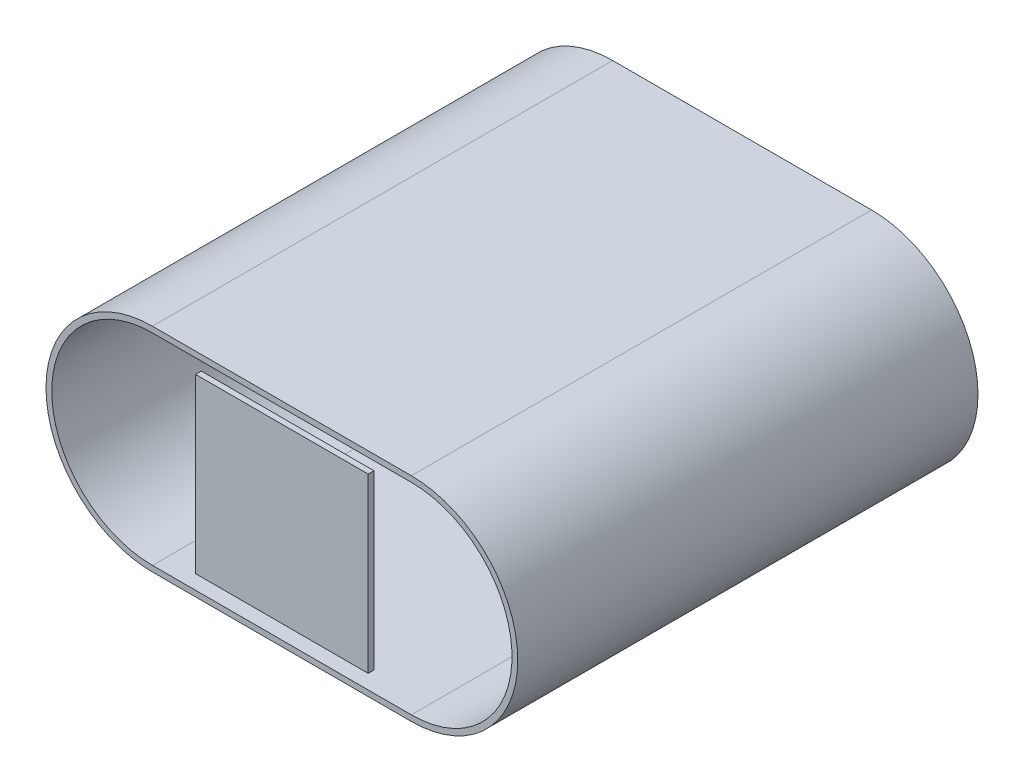
SolidWorks part; units mm, degrees
other "COLL.BOX-Boss-Extrude5"
other "COLL.BOX-Boss-Extrude4"
other "COLL.BOX-Boss-Extrude2"
ref_plane "Front Plane" through (0, 0, 0) normal (0, 0, 1) x (1, 0, 0)
ref_plane "Top Plane" through (0, 0, 0) normal (0, 1, 0) x (1, 0, 0)
ref_plane "Right Plane" through (0, 0, 0) normal (1, 0, 0) x (0, 0, -1)
sketch "Sketch1" plane through (0, 0, 0) normal (0, 0, 1) x (1, 0, 0)
  line L1 (-22.5, -18.5) -> (22.5, -18.5)
  line L2 (-22.5, -18.5) -> (-22.5, 18.5)
  line L3 (-22.5, 18.5) -> (22.5, 18.5)
  line L4 (22.5, -18.5) -> (22.5, 18.5)
  line L5 (-22.5, -18.5) -> (22.5, 18.5) construction
  line L6 (-22.5, 18.5) -> (22.5, -18.5) construction
  arc A0 (-22.5, 18.5) -> (-22.5, -18.5) centre (-22.5, 0) ccw
  arc A1 (22.5, 18.5) -> (22.5, -18.5) centre (22.5, 0) cw
  point P0 (0, 0)
  dimension "D1" = 37
  dimension "D2" = 45
extrude "Boss-Extrude1" add sketch "Sketch1" along normal blind 80 contours L1 L4 L3 L2 | A1 L4 | L2 A0
shell "Shell1" thickness 1
sketch "Sketch2" plane through (0, 0, 0) normal (0, 0, -1) x (-1, 0, 0)
  line L1 (-22.5, -17.5) -> (22.5, -17.5)
  line L2 (-22.5, -17.5) -> (-22.5, 17.5)
  line L3 (-22.5, 17.5) -> (22.5, 17.5)
  line L4 (22.5, -17.5) -> (22.5, 17.5)
  line L5 (-22.5, -17.5) -> (22.5, 17.5) construction
  line L6 (-22.5, 17.5) -> (22.5, -17.5) construction
  point P0 (0, 0)
  dimension "D1" = 35
  dimension "D2" = 45
extrude "Boss-Extrude2" add sketch "Sketch2" against normal blind 1 separate body
sketch "Sketch3" plane through (0, 0, 0) normal (0, 0, -1) x (-1, 0, 0)
  circle A0 centre (0, 0) radius 1.25
  dimension "D1" = 2.5
extrude "Boss-Extrude3" add sketch "Sketch3" along normal blind 15
ref_plane "Plane1" through (0, 0, -15) normal (0, 0, -1) x (-1, 0, 0)
ref_point "Point1"
sketch "Sketch5" plane through (0, 0, -15) normal (0, 0, -1) x (-1, 0, 0)
  line L0 (0, 2.4986) -> (0, -2.4986)
  arc A0 (0, 2.4986) -> (0, -2.4986) centre (0, 0) ccw
  dimension "D1" = 2.4986
revolve "Revolve1" add sketch "Sketch5" angle 360 about L0
sketch "Sketch6" plane through (0, 0, 0) normal (0, 0, -1) x (-1, 0, 0)
  line L1 (-22.5, -17.5) -> (22.5, -17.5)
  line L2 (-22.5, -17.5) -> (-22.5, 17.5)
  line L3 (-22.5, 17.5) -> (22.5, 17.5)
  line L4 (22.5, -17.5) -> (22.5, 17.5)
  line L5 (-22.5, -17.5) -> (22.5, 17.5) construction
  line L6 (-22.5, 17.5) -> (22.5, -17.5) construction
  point P0 (0, 0)
  dimension "D1" = 35
  dimension "D2" = 45
extrude "Boss-Extrude4" add sketch "Sketch6" against normal blind 1 separate body
sketch "Sketch7" plane through (0, 0, 80) normal (0, 0, 1) x (1, 0, 0)
  line L1 (-15, -15) -> (15, -15)
  line L2 (-15, -15) -> (-15, 15)
  line L3 (-15, 15) -> (15, 15)
  line L4 (15, -15) -> (15, 15)
  line L5 (-15, -15) -> (15, 15) construction
  line L6 (-15, 15) -> (15, -15) construction
  point P0 (0, 0)
  dimension "D1" = 30
extrude "Boss-Extrude5" add sketch "Sketch7" against normal blind 1 separate body
